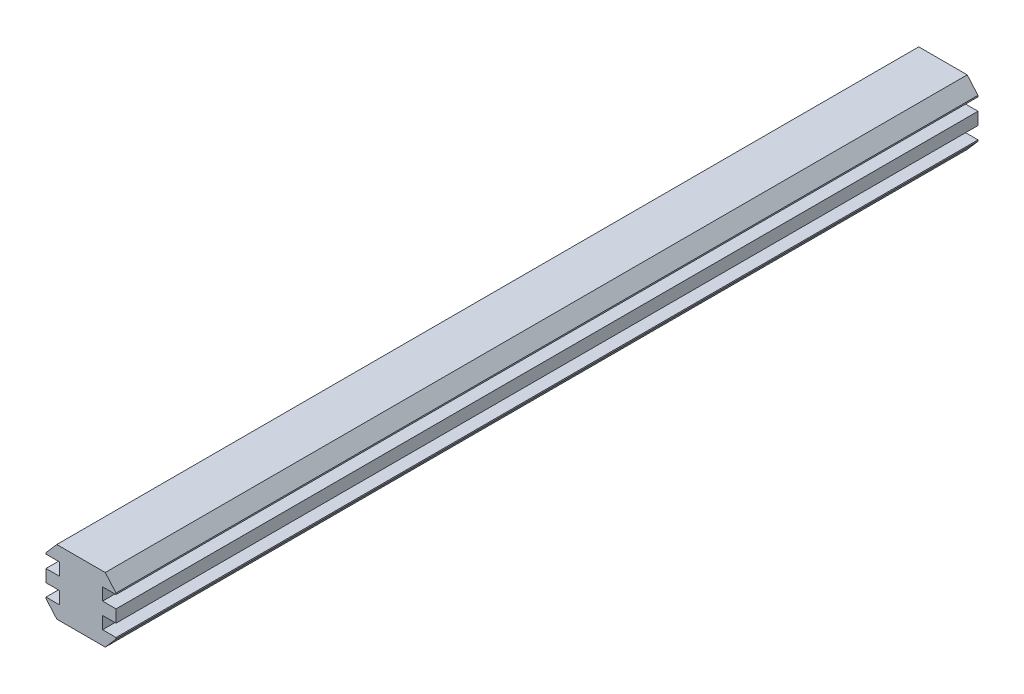
SolidWorks part; units mm, degrees
material "PE Alta Densidade"
ref_plane "Plano frontal" through (0, 0, 0) normal (0, 0, 1) x (1, 0, 0)
ref_plane "Plano superior" through (0, 0, 0) normal (0, 1, 0) x (1, 0, 0)
ref_plane "Plano direito" through (0, 0, 0) normal (1, 0, 0) x (0, 0, -1)
sketch "Esboço1" plane through (0, 0, 0) normal (0, 0, 1) x (1, 0, 0)
  line L0 (-4.5, -6) -> (4.5, -6)
  line L1 (-4.5, -6) -> (-6.5, -3.7)
  line L2 (6.5, -3.7) -> (6.5, -3.45)
  line L3 (6.5, -3.45) -> (4, -3.45)
  line L4 (4, -3.45) -> (4, -1.15)
  line L5 (4, -1.15) -> (6.5, -1.15)
  line L6 (6.5, -1.15) -> (6.5, 1.15)
  line L7 (4, 1.15) -> (6.5, 1.15)
  line L8 (4, 3.45) -> (4, 1.15)
  line L9 (6.5, 3.45) -> (4, 3.45)
  line L10 (6.5, 3.7) -> (6.5, 3.45)
  line L11 (4.5, -6) -> (6.5, -3.7)
  line L12 (4.5, 6) -> (6.5, 3.7)
  line L13 (0, 14.388) -> (0, -9.624) construction
  line L14 (-4.5, 6) -> (4.5, 6)
  line L15 (-6.5, -3.7) -> (-6.5, -3.45)
  line L16 (-6.5, -3.45) -> (-4, -3.45)
  line L17 (-4, -3.45) -> (-4, -1.15)
  line L18 (-4, -1.15) -> (-6.5, -1.15)
  line L19 (-6.5, -1.15) -> (-6.5, 1.15)
  line L20 (-4.5, 6) -> (-6.5, 3.7)
  line L21 (-6.5, 3.7) -> (-6.5, 3.45)
  line L22 (-6.5, 3.45) -> (-4, 3.45)
  line L23 (-4, 3.45) -> (-4, 1.15)
  line L24 (-4, 1.15) -> (-6.5, 1.15)
  line L25 (-8.8286, 0) -> (11.4625, 0) construction
  point P0 (0, 0)
  point P1 (6.5, -6)
  point P17 (-6.5, -6)
  point P31 (6.5, 0)
  point P33 (0, -6)
  dimension "D1" = 12
  dimension "D2" = 13
  dimension "D3" = 2.3
  dimension "D4" = 2.3
  dimension "D5" = 0.25
  dimension "D6" = 8
  dimension "D7" = 9
extrude "Ressalto-extrusão1" add sketch "Esboço1" along normal blind 160
